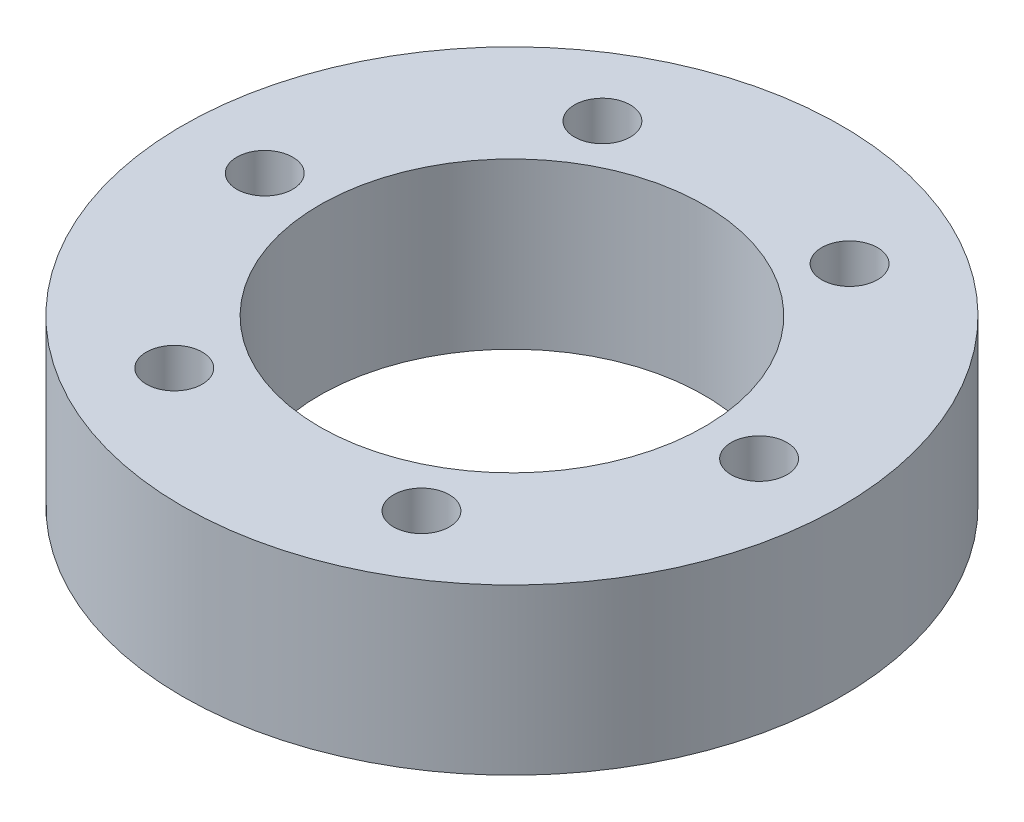
SolidWorks part; units mm, degrees
ref_plane "前视基准面" through (0, 0, 0) normal (0, 0, 1) x (1, 0, 0)
ref_plane "上视基准面" through (0, 0, 0) normal (0, 1, 0) x (1, 0, 0)
ref_plane "右视基准面" through (0, 0, 0) normal (1, 0, 0) x (0, 0, -1)
other "Configuration Table"
sketch "草图1" plane through (0, 0, 0) normal (0, 1, 0) x (1, 0, 0)
  circle A0 centre (0, 0) radius 18
  dimension "D1" = 36
extrude "凸台-拉伸1" add sketch "草图1" along normal blind 9
sketch "草图2" plane through (0, 9, 0) normal (0, 1, 0) x (1, 0, 0)
  circle A0 centre (0, 0) radius 13.5 construction
  circle A1 centre (13.5, 0) radius 1.525
  circle A2 centre (6.75, -11.6913) radius 1.525
  circle A3 centre (-6.75, -11.6913) radius 1.525
  circle A4 centre (-13.5, 0) radius 1.525
  circle A5 centre (-6.75, 11.6913) radius 1.525
  circle A6 centre (6.75, 11.6913) radius 1.525
  point P17 (0, 0)
  dimension "D1" = 27
  dimension "D2" = 3.05
  dimension "D3" = 6
extrude "切除-拉伸1" cut sketch "草图2" against normal through all
sketch "草图3" plane through (0, 9, 0) normal (0, 1, 0) x (1, 0, 0)
  circle A0 centre (0, 0) radius 10.5
  dimension "D1" = 21
extrude "切除-拉伸2" cut sketch "草图3" against normal through all
